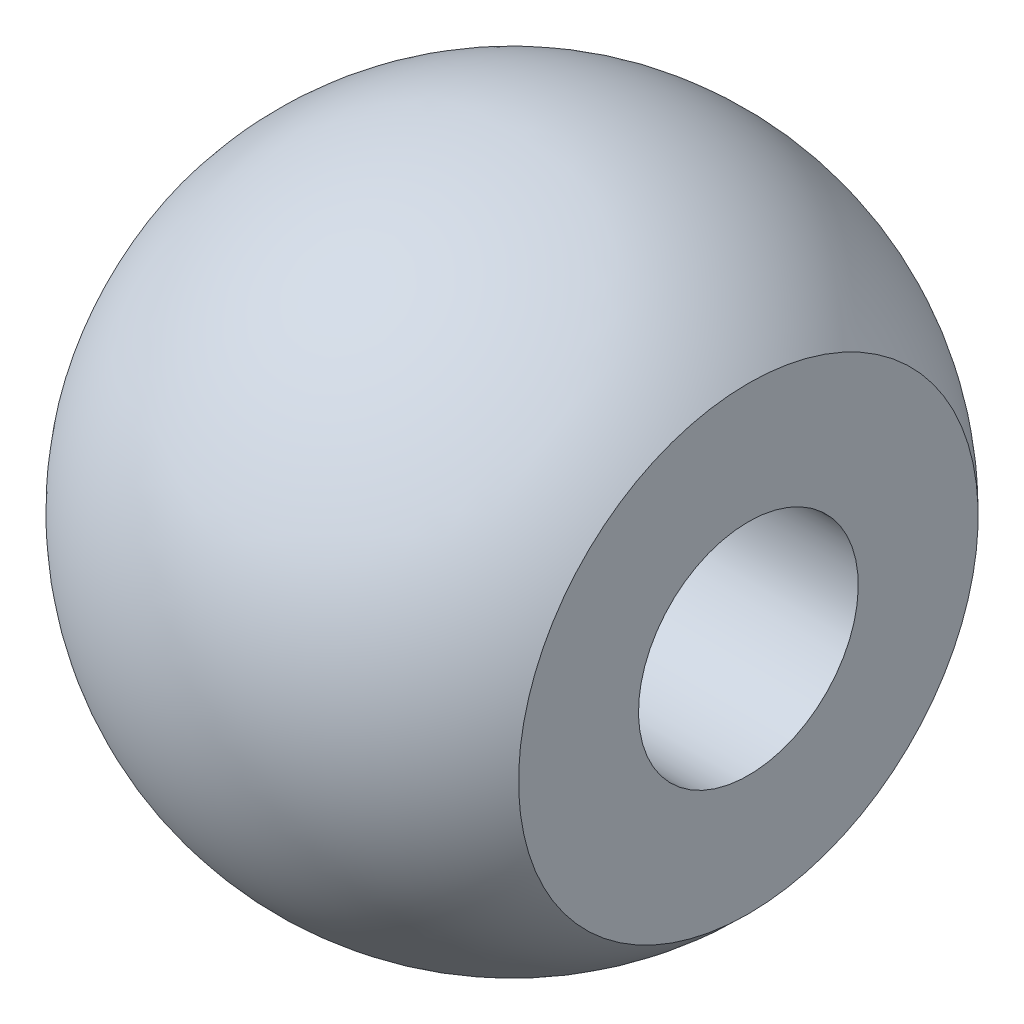
SolidWorks part; units mm, degrees
ref_plane "Front Plane" through (0, 0, 0) normal (0, 0, 1) x (1, 0, 0)
ref_plane "Top Plane" through (0, 0, 0) normal (0, 1, 0) x (1, 0, 0)
ref_plane "Right Plane" through (0, 0, 0) normal (1, 0, 0) x (0, 0, -1)
sketch "Sketch1" plane through (0, 0, 0) normal (0, 0, 1) x (1, 0, 0)
  line L0 (0.6203, 0) -> (-15.5304, 0) construction
  line L5 (-3.6981, -2) -> (4.3019, -2)
  line L6 (4.3019, -4.1825) -> (4.3019, -2)
  line L7 (-3.6981, -2) -> (-4.6981, -3.7321)
  arc A1 (-4.6981, -3.7321) -> (4.3019, -4.1825) centre (0, 0) ccw
  dimension "D2" = 1
  dimension "D5" = 6
  dimension "D1" = 9
  dimension "D3" = 4
  dimension "D4" = 60
revolve "Revolve1" add sketch "Sketch1" angle 360 about L0
